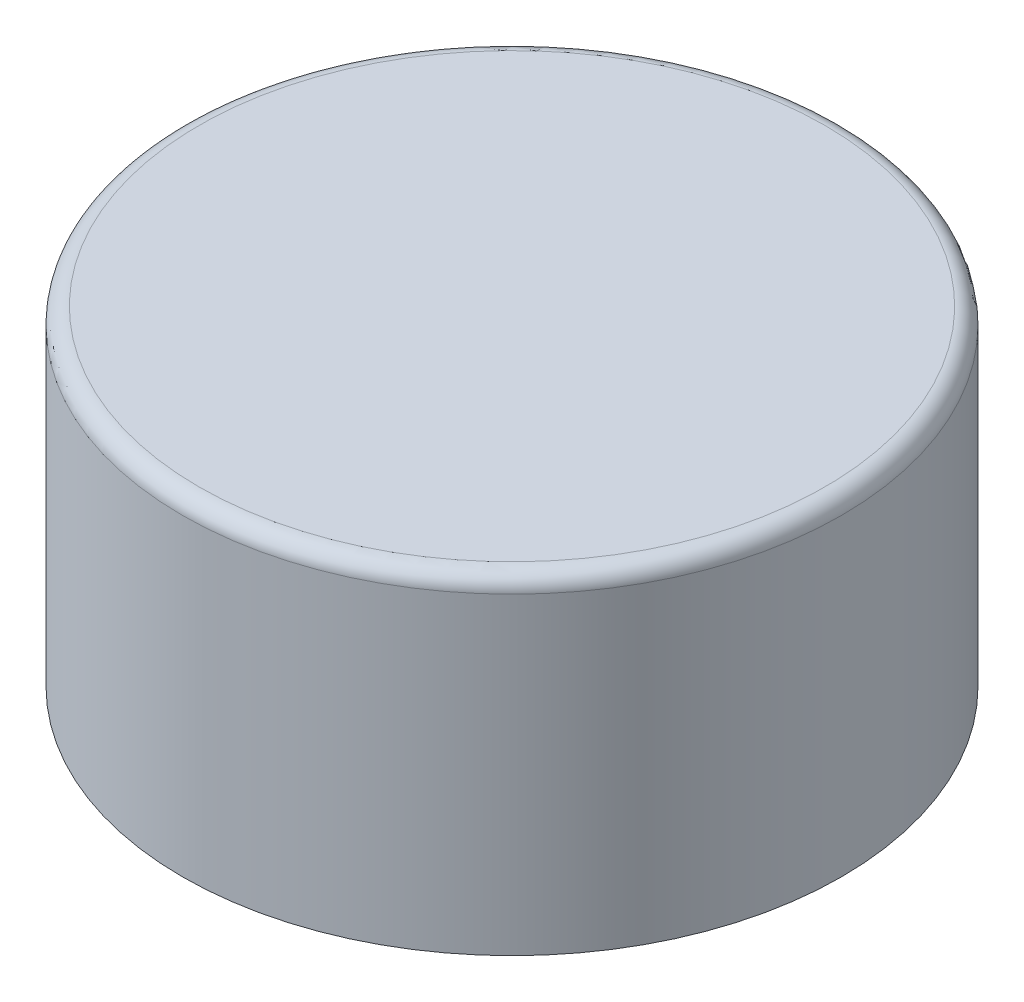
SolidWorks part; units mm, degrees
material "Ge"
ref_plane "前视基准面" through (0, 0, 0) normal (0, 0, 1) x (1, 0, 0)
ref_plane "上视基准面" through (0, 0, 0) normal (0, 1, 0) x (1, 0, 0)
ref_plane "右视基准面" through (0, 0, 0) normal (1, 0, 0) x (0, 0, -1)
sketch "草图1" plane through (0, 0, 0) normal (0, 1, 0) x (1, 0, 0)
  circle A0 centre (0, 0) radius 40
extrude "凸台-拉伸1" add sketch "草图1" along normal mid plane 40
fillet "圆角1" radius 2 1 edges at (0, 20, 40)
sketch "草图2" plane through (0, 0, 0) normal (0, 0, 1) x (1, 0, 0)
  line L1 (0, 0) -> (0.5, 0)
  line L6 (0, 0) -> (0, 1)
  line L7 (0, 1) -> (0.5, 1)
  line L8 (0.5, 0) -> (0.5, 1)
  line L9 (0, 0) -> (0.5, 1) construction
  line L10 (0, 1) -> (0.5, 0) construction
  point P4 (0.25, 0.5)
sketch "草图3" plane through (0, -20, 0) normal (0, -1, 0) x (1, 0, 0)
  circle A0 centre (0, 0) radius 9
sweep "切除-扫描3" cut path "草图3" circular profile diameter 1.5 parameters "D3"=1.5
revolve "切除-旋转1" cut sketch "草图2" angle 360 about L6
sketch "草图5" plane through (0, -20, 0) normal (0, -1, 0) x (1, 0, 0)
  line L0 (0, 0) -> (40, 0)
  circle A0 centre (0, 0) radius 40 construction
